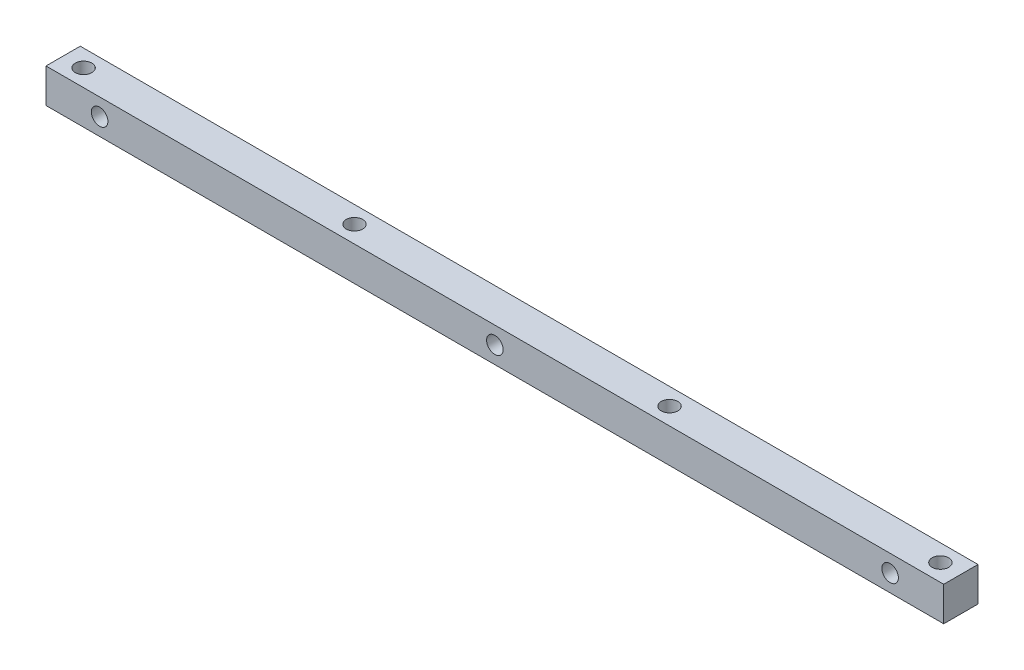
SolidWorks part; units mm, degrees
ref_plane "Alzado" through (0, 0, 0) normal (0, 0, 1) x (1, 0, 0)
ref_plane "Planta" through (0, 0, 0) normal (0, 1, 0) x (1, 0, 0)
ref_plane "Vista lateral" through (0, 0, 0) normal (1, 0, 0) x (0, 0, -1)
sketch "Croquis1" plane through (0, 0, 0) normal (0, 0, 1) x (1, 0, 0)
  line L0 (-81.2, 0) -> (81.2, 0) construction
  line L1 (81.2, -3.1) -> (-81.2, -3.1)
  line L2 (81.2, -3.1) -> (81.2, 3.1)
  line L3 (81.2, 3.1) -> (-81.2, 3.1)
  line L4 (-81.2, -3.1) -> (-81.2, 3.1)
  line L5 (81.2, -3.1) -> (-81.2, 3.1) construction
  line L6 (81.2, 3.1) -> (-81.2, -3.1) construction
  circle A0 centre (0, 0) radius 2.9 construction
  circle A1 centre (-71.5, 0) radius 2.9 construction
  circle A2 centre (71.5, 0) radius 2.9 construction
  circle A3 centre (-71.5, 0) radius 1.5
  circle A4 centre (0, 0) radius 1.5
  circle A5 centre (71.5, 0) radius 1.5
  point P0 (0, 0)
  point P12 (-74.4, 0)
  point P15 (74.4, 0)
  point P16 (-68.6, 0)
  point P17 (2.9, 0)
  point P18 (-2.9, 0)
  point P19 (68.6, 0)
  dimension "D2" = 5.8
  dimension "D6" = 3
  dimension "D1" = 6.2
  dimension "D3" = 6.8
  dimension "D4" = 6.8
  dimension "D5" = 71.5
extrude "Saliente-Extruir1" add sketch "Croquis1" along normal blind 6.2
sketch "Croquis2" plane through (0, 3.1, 0) normal (0, 1, 0) x (1, 0, 0)
  line L0 (-81.2, -3.1) -> (81.2, -3.1) construction
  line L1 (-81.2, -6.2) -> (-81.2, 0) construction
  line L2 (81.2, -6.2) -> (81.2, 0) construction
  line L3 (80.4, -3.1) -> (81.2, -3.1) construction
  line L4 (-81.2, -3.1) -> (-80.4, -3.1) construction
  circle A0 centre (-77.5, -3.1) radius 2.9 construction
  circle A1 centre (-28.5, -3.1) radius 2.9 construction
  circle A2 centre (28.5, -3.1) radius 2.9 construction
  circle A3 centre (77.5, -3.1) radius 2.9 construction
  circle A4 centre (-77.5, -3.1) radius 1.5
  circle A5 centre (-28.5, -3.1) radius 1.5
  circle A6 centre (28.5, -3.1) radius 1.5
  circle A7 centre (77.5, -3.1) radius 1.5
  point P14 (25.6, -3.1)
  point P15 (31.4, -3.1)
  point P16 (74.6, -3.1)
  point P17 (80.4, -3.1)
  point P18 (-31.4, -3.1)
  point P19 (-25.6, -3.1)
  point P20 (-74.6, -3.1)
  point P21 (-80.4, -3.1)
  dimension "D1" = 5.8
  dimension "D6" = 3
  dimension "D2" = 49
  dimension "D4" = 57
  dimension "D5" = 49
extrude "Cortar-Extruir1" cut sketch "Croquis2" against normal blind 6.2
